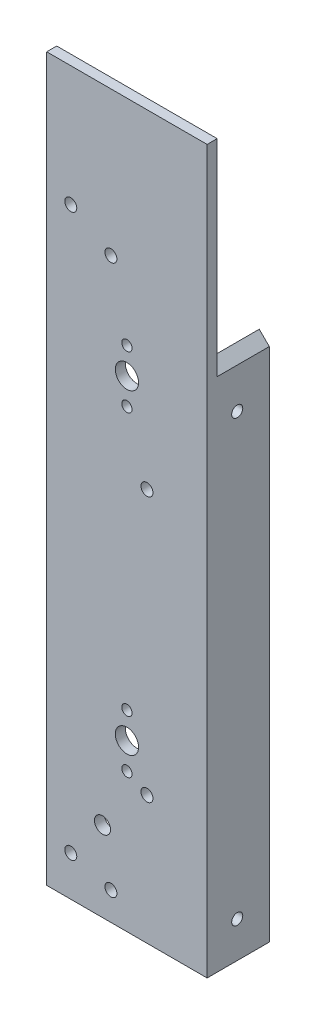
SolidWorks part; units mm, degrees
ref_plane "Front Plane" through (0, 0, 0) normal (0, 0, 1) x (1, 0, 0)
ref_plane "Top Plane" through (0, 0, 0) normal (0, 1, 0) x (1, 0, 0)
ref_plane "Right Plane" through (0, 0, 0) normal (1, 0, 0) x (0, 0, -1)
sketch "Sketch1" plane through (0, 0, 0) normal (0, 1, 0) x (1, 0, 0)
  line L0 (0, 0) -> (-50.8, 0)
  line L1 (-50.8, 0) -> (-50.8, 3.175)
  line L2 (-50.8, 3.175) -> (-3.175, 3.175)
  line L3 (-3.175, 3.175) -> (-3.175, 19.685)
  line L4 (-3.175, 19.685) -> (0, 19.685)
  line L5 (0, 19.685) -> (0, 0)
  dimension "D1" = 16.51
  dimension "D2" = 3.175
  dimension "D3" = 50.8
extrude "Boss-Extrude1" add sketch "Sketch1" along normal blind 203.2 contours L2 L3 L4 L5 L0 L1
sketch "Sketch4" plane through (0, 0, 0) normal (0, 0, 1) x (1, 0, 0)
  line L0 (0, 203.2) -> (0, 0) construction
  line L1 (-50.8, 214.122) -> (-57.2505, 214.122)
  line L2 (-50.8, 214.122) -> (0, 163.322)
  line L3 (-50.8, 203.2) -> (-50.8, 0) construction
  line L5 (14.4916, 163.322) -> (14.4916, 247.072)
  line L6 (14.4916, 247.072) -> (-57.2505, 247.072)
  line L7 (-57.2505, 247.072) -> (-57.2505, 214.122)
  line L9 (0, 163.322) -> (14.4916, 163.322)
  dimension "D1" = 163.322
  dimension "D2" = 135
extrude "Cut-Extrude2" cut sketch "Sketch4" against normal through all contours L7 L1 L2 L9 L5 L6
sketch "Sketch5" plane through (0, 0, 0) normal (0, 0, 1) x (1, 0, 0)
  line L0 (-25.4, 160.782) -> (-25.4, 144.018) construction
  line L1 (0, 0) -> (-50.8, 0) construction
  line L2 (0, 152.4) -> (-50.8, 152.4) construction
  line L3 (0, 163.322) -> (0, 0) construction
  line L4 (-50.8, 203.2) -> (-50.8, 0) construction
  circle A0 centre (-25.4, 152.4) radius 3.683
  circle A1 centre (-25.4, 160.782) radius 1.632
  circle A2 centre (-25.4, 144.018) radius 1.632
  point P4 (-25.4, 152.4)
  point P15 (-25.4, 152.4)
  dimension "D1" = 7.366
  dimension "D2" = 3.2639
  dimension "D3" = 152.4
  dimension "D4" = 16.764
extrude "Cut-Extrude3" cut sketch "Sketch5" against normal through all
sketch "Sketch6" plane through (0, 0, 0) normal (1, 0, 0) x (0, 0, -1)
  line L1 (19.685, 163.322) -> (0, 163.322) construction
  line L3 (19.685, 0) -> (0, 0) construction
  circle A0 centre (9.5305, 11.43) radius 1.7526
  circle A1 centre (9.5305, 150.622) radius 1.7526
  dimension "D1" = 3.5052
  dimension "D4" = 3.5052
  dimension "D2" = 11.43
  dimension "D3" = 12.7
extrude "Cut-Extrude4" cut sketch "Sketch6" against normal through all contours A1 | A0
sketch "Sketch7" plane through (0, 0, -3.175) normal (0, 0, -1) x (-1, 0, 0)
  circle A0 centre (30.48, 8.89) radius 1.7526
  circle A1 centre (30.48, 8.89) radius 1.7526 construction
  circle A2 centre (30.48, 182.88) radius 1.7526
  circle A3 centre (30.48, 182.88) radius 1.7526 construction
sketch "Sketch8" plane through (0, 0, -3.175) normal (0, 0, -1) x (-1, 0, 0)
  circle A0 centre (30.48, 8.89) radius 1.8986
  circle A1 centre (30.48, 8.89) radius 1.7526 construction
  circle A2 centre (30.48, 182.88) radius 1.8987
  circle A3 centre (30.48, 182.88) radius 1.7526 construction
  dimension "D1" = 3.7973
  dimension "D2" = 3.7973
extrude "Cut-Extrude5" cut sketch "Sketch8" against normal through all
sketch "Sketch9" plane through (0, 0, -3.175) normal (0, 0, -1) x (-1, 0, 0)
  line L0 (0, 163.322) -> (0, 0) construction
  line L2 (0, 0) -> (50.8, 0) construction
  circle A0 centre (19.05, 40.64) radius 1.8987
  circle A1 centre (19.05, 124.46) radius 1.8987
  dimension "D1" = 3.7973
  dimension "D2" = 19.05
  dimension "D3" = 83.82
  dimension "D4" = 40.64
extrude "Cut-Extrude6" cut sketch "Sketch9" against normal through all
sketch "Sketch10" plane through (0, 0, 0) normal (0, 0, 1) x (1, 0, 0)
  line L0 (0, 228.6) -> (0, 163.322)
  line L1 (-50.8, 203.2) -> (-39.878, 203.2)
  line L2 (-50.8, 203.2) -> (-50.8, 228.6)
  line L3 (-50.8, 228.6) -> (0, 228.6)
  line L5 (0, 163.322) -> (-39.878, 203.2)
  line L6 (-39.878, 203.2) -> (0, 163.322) construction
  dimension "D1" = 25.4
extrude "Boss-Extrude2" add sketch "Sketch10" against normal blind 3.175
sketch "Sketch11" plane through (0, 0, 0) normal (0, 0, 1) x (1, 0, 0)
  line L1 (-50.8, 228.6) -> (-50.8, 0) construction
  line L2 (0, 0) -> (-50.8, 0) construction
  circle A0 centre (-33.1362, 25.4) radius 2.54
  dimension "D3" = 5.08
  dimension "D1" = 17.6638
  dimension "D2" = 25.4
extrude "Cut-Extrude7" cut sketch "Sketch11" against normal through all
sketch "Sketch12" plane through (0, 0, -3.175) normal (0, 0, -1) x (-1, 0, 0)
  circle A0 centre (43.18, 12.7) radius 1.8986
  circle A1 centre (43.18, 190.4989) radius 1.8987
extrude "Cut-Extrude8" cut sketch "Sketch12" against normal through all
sketch "Sketch13" plane through (0, 0, 0) normal (0, 0, 1) x (1, 0, 0)
  circle A0 centre (-25.4, 52.4) radius 3.683
  circle A1 centre (-25.4, 152.4) radius 3.683 construction
  circle A2 centre (-25.4, 60.782) radius 1.632
  circle A3 centre (-25.4, 44.018) radius 1.632
  circle A4 centre (-25.4, 144.018) radius 1.632 construction
  point P6 (-25.4, 152.4)
  point P12 (0, 0)
  point P13 (0, 0)
  dimension "D1" = 100
  dimension "D2" = 8.382
  dimension "D3" = 8.382
extrude "Cut-Extrude9" cut sketch "Sketch13" against normal through all and the other way through all
